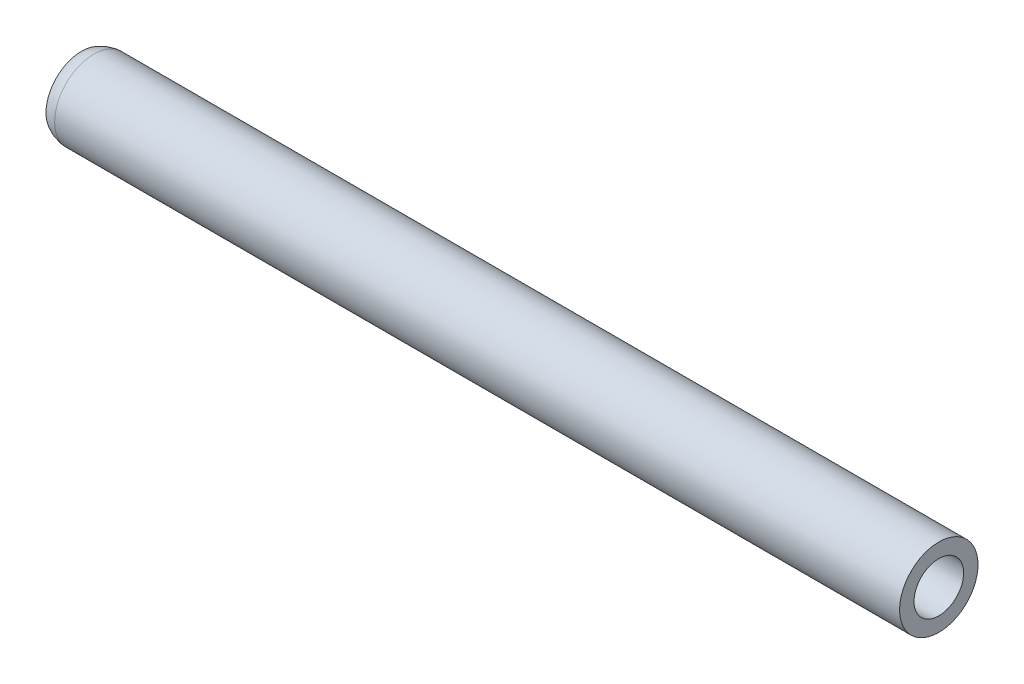
SolidWorks part; units mm, degrees
ref_plane "Front Plane" through (0, 0, 0) normal (0, 0, 1) x (1, 0, 0)
ref_plane "Top Plane" through (0, 0, 0) normal (0, 1, 0) x (1, 0, 0)
ref_plane "Right Plane" through (0, 0, 0) normal (1, 0, 0) x (0, 0, -1)
sketch "Sketch1" plane through (0, 0, 0) normal (1, 0, 0) x (0, 0, -1)
  circle A0 centre (0, 0) radius 16.256
  circle A1 centre (0, 0) radius 10.287
  dimension "D1" = 32.512
  dimension "D2" = 20.574
extrude "Boss-Extrude1" add sketch "Sketch1" along normal blind 177.8 and the other way blind 177.8
sketch "Sketch3" plane through (0, 0, 0) normal (0, 1, 0) x (1, 0, 0)
  line L0 (-177.8, 16.256) -> (-171.45, 16.256)
  line L1 (177.8, 16.256) -> (-177.8, 16.256) construction
  line L2 (-177.8, 16.256) -> (-177.8, 14.732)
  line L3 (-177.8, 16.256) -> (-177.8, -16.256) construction
  line L4 (-177.8, 0) -> (-161.6946, 0)
  line L5 (-55, 0) -> (55, 0) construction
  arc A0 (-177.8, 14.732) -> (-171.45, 16.256) centre (-172.0687, 4.8428) cw
  point P9 (-184.796, 8.6634)
  dimension "D1" = 1.524
  dimension "D3" = 11.43
  dimension "D2" = 6.35
  dimension "D4" = 16.1054
revolve "Cut-Revolve1" cut sketch "Sketch3" angle 360 about L4
